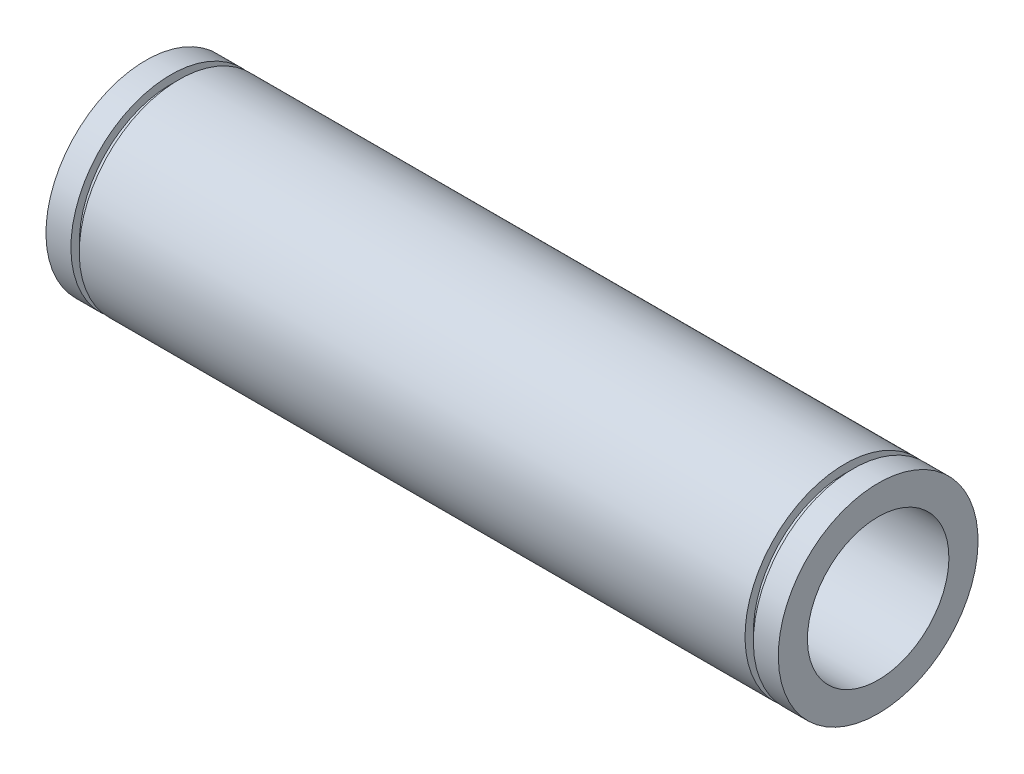
SolidWorks part; units mm, degrees
material "1023 Karbon Çeliği Levha (SS)"
ref_plane "Ön Düzlem" through (0, 0, 0) normal (0, 0, 1) x (1, 0, 0)
ref_plane "Üst Düzlem" through (0, 0, 0) normal (0, 1, 0) x (1, 0, 0)
ref_plane "Sağ Düzlem" through (0, 0, 0) normal (1, 0, 0) x (0, 0, -1)
sketch "Çizim1" plane through (0, 0, 0) normal (0, 0, 1) x (1, 0, 0)
  line L0 (44, 0) -> (-44, 0) construction
  line L1 (-44, 0) -> (-44, 12)
  line L2 (-44, 12) -> (-41, 12)
  line L3 (44, 12) -> (44, 0)
  line L4 (44, 12) -> (41, 12) construction
  line L5 (41, 12) -> (41, 11)
  line L6 (41, 11) -> (40, 11)
  line L7 (40, 11) -> (40, 12)
  line L8 (41, 12) -> (44, 12)
  line L9 (0, 0) -> (0, 12) construction
  line L10 (-40, 11) -> (-40, 12)
  line L11 (-41, 11) -> (-40, 11)
  line L12 (-41, 12) -> (-41, 11)
  line L13 (-40, 12) -> (40, 12)
  line L14 (-44, 0) -> (44, 0)
  point P4 (0, 0)
  dimension "D1" = 12
  dimension "D2" = 88
  dimension "D3" = 44
  dimension "D4" = 3
  dimension "D5" = 1
  dimension "D6" = 1
revolve "Döndür1" add sketch "Çizim1" angle 360 about L14
sketch "Çizim2" plane through (44, 0, 0) normal (1, 0, 0) x (0, 0, -1)
  circle A0 centre (0, 0) radius 8.5
  dimension "D1" = 17
extrude "Kes-Ekstrüzyon1" cut sketch "Çizim2" against normal through all
